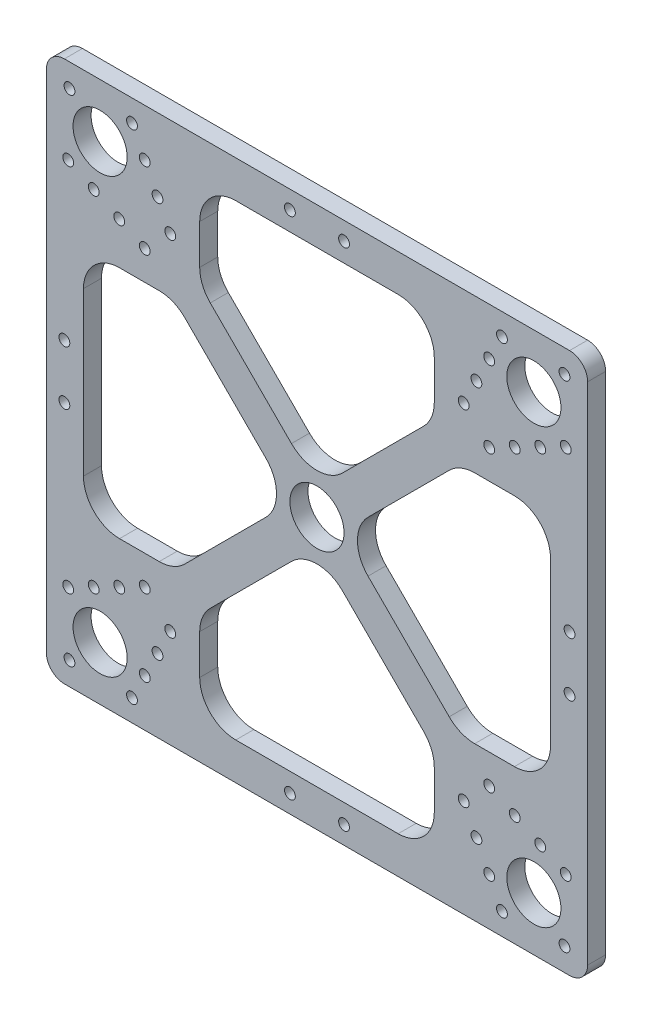
SolidWorks part; units mm, degrees
ref_plane "Front Plane" through (0, 0, 0) normal (0, 0, 1) x (1, 0, 0)
ref_plane "Top Plane" through (0, 0, 0) normal (0, 1, 0) x (1, 0, 0)
ref_plane "Right Plane" through (0, 0, 0) normal (1, 0, 0) x (0, 0, -1)
sketch "Sketch1" plane through (0, 0, 0) normal (0, 0, 1) x (1, 0, 0)
  line L1 (70, 75) -> (-70, 75)
  line L2 (75, 70) -> (75, -70)
  line L3 (70, -75) -> (-70, -75)
  line L4 (-75, 70) -> (-75, -70)
  line L5 (75, 75) -> (-75, -75) construction
  line L6 (75, -75) -> (-75, 75) construction
  line L27 (-7.5, 70) -> (7.5, 70) construction
  line L28 (40.6586, 47.7297) -> (47.7297, 40.6586) construction
  line L29 (51.2652, 68.9429) -> (68.9429, 51.2652) construction
  line L30 (44.1942, 54.8008) -> (54.8008, 44.1942) construction
  line L31 (47.7297, 61.8718) -> (61.8718, 47.7297) construction
  line L32 (14.1421, 7.0711) -> (36.6421, 29.5711)
  line L33 (54.7132, 32.5) -> (43.7132, 32.5)
  line L34 (64.7132, 22.5) -> (64.7132, -22.5)
  line L35 (54.7132, -32.5) -> (43.7132, -32.5)
  line L37 (-22.5, 64.7132) -> (22.5, 64.7132)
  line L38 (-32.5, 54.7132) -> (-32.5, 43.7132)
  line L39 (32.5, 54.7132) -> (32.5, 43.7132)
  line L40 (-7.0711, 14.1421) -> (-29.5711, 36.6421)
  line L41 (36.6421, -29.5711) -> (14.1421, -7.0711)
  line L42 (7.0711, -14.1421) -> (29.5711, -36.6421)
  line L43 (32.5, -54.7132) -> (32.5, -43.7132)
  line L44 (29.5711, 36.6421) -> (7.0711, 14.1421)
  line L45 (22.5, -64.7132) -> (-22.5, -64.7132)
  line L46 (-32.5, -54.7132) -> (-32.5, -43.7132)
  line L47 (-29.5711, -36.6421) -> (-7.0711, -14.1421)
  line L48 (-14.1421, -7.0711) -> (-36.6421, -29.5711)
  line L49 (-54.7132, -32.5) -> (-43.7132, -32.5)
  line L50 (-64.7132, -22.5) -> (-64.7132, 22.5)
  line L51 (-54.7132, 32.5) -> (-43.7132, 32.5)
  line L52 (-36.6421, 29.5711) -> (-14.1421, 7.0711)
  circle A0 centre (-60.1041, 60.1041) radius 7.5
  circle A1 centre (60.1041, 60.1041) radius 7.5
  circle A2 centre (60.1041, -60.1041) radius 7.5
  circle A3 centre (-60.1041, -60.1041) radius 7.5
  circle A4 centre (0, 0) radius 7.5
  arc A5 (75, -70) -> (70, -75) centre (70, -70) cw
  arc A6 (-70, -75) -> (-75, -70) centre (-70, -70) cw
  arc A7 (70, 75) -> (75, 70) centre (70, 70) cw
  arc A8 (-70, 75) -> (-75, 70) centre (-70, 70) ccw
  circle A29 centre (-7.5, 70) radius 1.5
  circle A30 centre (7.5, 70) radius 1.5
  circle A31 centre (70, 7.5) radius 1.5
  circle A32 centre (70, -7.5) radius 1.5
  circle A33 centre (7.5, -70) radius 1.5
  circle A34 centre (-7.5, -70) radius 1.5
  circle A35 centre (-70, -7.5) radius 1.5
  circle A36 centre (-70, 7.5) radius 1.5
  circle A37 centre (40.6586, 47.7297) radius 1.5
  circle A38 centre (47.7297, 40.6586) radius 1.5
  circle A39 centre (44.1942, 54.8008) radius 1.5
  circle A40 centre (54.8008, 44.1942) radius 1.5
  circle A41 centre (61.8718, 47.7297) radius 1.5
  circle A42 centre (47.7297, 61.8718) radius 1.5
  circle A43 centre (51.2652, 68.9429) radius 1.5
  circle A44 centre (68.9429, 51.2652) radius 1.5
  circle A45 centre (47.7297, -40.6586) radius 1.5
  circle A46 centre (54.8008, -44.1942) radius 1.5
  circle A47 centre (61.8718, -47.7297) radius 1.5
  circle A48 centre (68.9429, -51.2652) radius 1.5
  circle A49 centre (51.2652, -68.9429) radius 1.5
  circle A50 centre (47.7297, -61.8718) radius 1.5
  circle A51 centre (44.1942, -54.8008) radius 1.5
  circle A52 centre (40.6586, -47.7297) radius 1.5
  circle A53 centre (-40.6586, -47.7297) radius 1.5
  circle A54 centre (-44.1942, -54.8008) radius 1.5
  circle A55 centre (-47.7297, -61.8718) radius 1.5
  circle A56 centre (-51.2652, -68.9429) radius 1.5
  circle A57 centre (-68.9429, -51.2652) radius 1.5
  circle A58 centre (-61.8718, -47.7297) radius 1.5
  circle A59 centre (-54.8008, -44.1942) radius 1.5
  circle A60 centre (-47.7297, -40.6586) radius 1.5
  circle A61 centre (-47.7297, 40.6586) radius 1.5
  circle A62 centre (-54.8008, 44.1942) radius 1.5
  circle A63 centre (-61.8718, 47.7297) radius 1.5
  circle A64 centre (-68.9429, 51.2652) radius 1.5
  circle A65 centre (-51.2652, 68.9429) radius 1.5
  circle A66 centre (-47.7297, 61.8718) radius 1.5
  circle A67 centre (-44.1942, 54.8008) radius 1.5
  circle A68 centre (-40.6586, 47.7297) radius 1.5
  circle A69 centre (68.5894, 68.5894) radius 1.5
  circle A70 centre (68.5894, -68.5894) radius 1.5
  circle A71 centre (-68.5894, -68.5894) radius 1.5
  circle A72 centre (-68.5894, 68.5894) radius 1.5
  arc A73 (-22.5, 64.7132) -> (-32.5, 54.7132) centre (-22.5, 54.7132) ccw
  arc A74 (22.5, 64.7132) -> (32.5, 54.7132) centre (22.5, 54.7132) cw
  arc A75 (29.5711, 36.6421) -> (32.5, 43.7132) centre (22.5, 43.7132) ccw
  arc A76 (-29.5711, 36.6421) -> (-32.5, 43.7132) centre (-22.5, 43.7132) cw
  arc A77 (-7.0711, 14.1421) -> (7.0711, 14.1421) centre (0, 21.2132) ccw
  arc A78 (14.1421, 7.0711) -> (14.1421, -7.0711) centre (21.2132, 0) ccw
  arc A79 (36.6421, 29.5711) -> (43.7132, 32.5) centre (43.7132, 22.5) cw
  arc A80 (64.7132, 22.5) -> (54.7132, 32.5) centre (54.7132, 22.5) ccw
  arc A81 (64.7132, -22.5) -> (54.7132, -32.5) centre (54.7132, -22.5) cw
  arc A82 (36.6421, -29.5711) -> (43.7132, -32.5) centre (43.7132, -22.5) ccw
  arc A83 (7.0711, -14.1421) -> (-7.0711, -14.1421) centre (0, -21.2132) ccw
  arc A84 (29.5711, -36.6421) -> (32.5, -43.7132) centre (22.5, -43.7132) cw
  arc A85 (22.5, -64.7132) -> (32.5, -54.7132) centre (22.5, -54.7132) ccw
  arc A86 (-22.5, -64.7132) -> (-32.5, -54.7132) centre (-22.5, -54.7132) cw
  arc A87 (-29.5711, -36.6421) -> (-32.5, -43.7132) centre (-22.5, -43.7132) ccw
  arc A88 (-14.1421, -7.0711) -> (-14.1421, 7.0711) centre (-21.2132, 0) ccw
  arc A89 (-36.6421, -29.5711) -> (-43.7132, -32.5) centre (-43.7132, -22.5) cw
  arc A90 (-64.7132, -22.5) -> (-54.7132, -32.5) centre (-54.7132, -22.5) ccw
  arc A91 (-64.7132, 22.5) -> (-54.7132, 32.5) centre (-54.7132, 22.5) cw
  arc A92 (-36.6421, 29.5711) -> (-43.7132, 32.5) centre (-43.7132, 22.5) ccw
  point P0 (0, 0)
  point P42 (0, 64.7132)
  point P55 (32.5, 39.5711)
  point P58 (-32.5, 39.5711)
  point P95 (0, 0)
  point P96 (0, 70)
  point P100 (44.1942, 44.1942)
  point P113 (0, 0)
  point P117 (60.1041, 60.1041)
  point P120 (49.4975, 49.4975)
  point P123 (54.8008, 54.8008)
  point P182 (0, 0)
  point P184 (0, 0)
  point P191 (0, 0)
  dimension "D4" = 15
  dimension "D5" = 15
  dimension "10" = 5
  dimension "D9" = 11
  dimension "D15" = 3
  dimension "D23" = 4
  dimension "3" = 3
  dimension "D8" = 10
  dimension "D1" = 150
  dimension "D2" = 150
  dimension "D3" = 85
  dimension "D7" = 4
  dimension "D10" = 45
  dimension "D6" = 5
  dimension "D13" = 15
  dimension "D14" = 4
  dimension "5" = 5
  dimension "D16" = 10
  dimension "D17" = 15
  dimension "D18" = 20
  dimension "D19" = 25
  dimension "D20" = 7.5
  dimension "D21" = 7.5
  dimension "D22" = 7.5
  dimension "D24" = 12
  dimension "D25" = 4
extrude "Boss-Extrude1" add sketch "Sketch1" along normal blind 5
